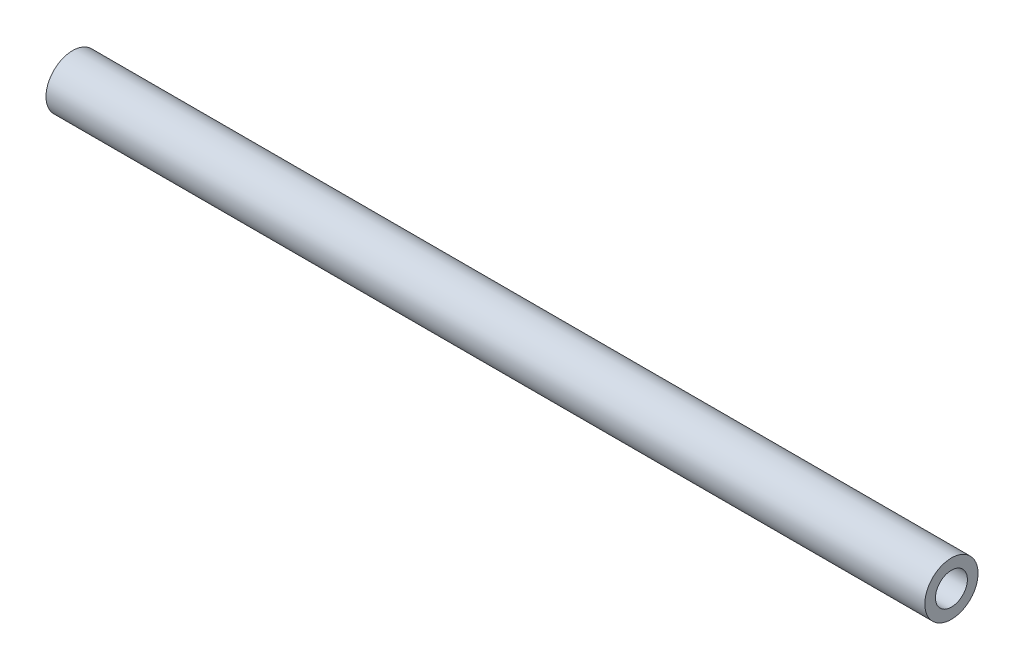
SolidWorks part; units mm, degrees
ref_plane "Front Plane" through (0, 0, 0) normal (0, 0, 1) x (1, 0, 0)
ref_plane "Top Plane" through (0, 0, 0) normal (0, 1, 0) x (1, 0, 0)
ref_plane "Right Plane" through (0, 0, 0) normal (1, 0, 0) x (0, 0, -1)
ref_plane "Plane1" through (0, 0, 0) normal (0, 0, -1) x (-1, 0, 0)
sketch "Sketch1" plane through (0, 0, 0) normal (0, 0, -1) x (-1, 0, 0)
  line L0 (0, 3) -> (0, 5)
  line L1 (0, 5) -> (-165, 5)
  line L2 (-165, 5) -> (-165, 3)
  line L3 (-165, 3) -> (0, 3)
  line L4 (-165, 0) -> (0, 0) construction
revolve "Revolve1" add sketch "Sketch1" angle 360 about L4
